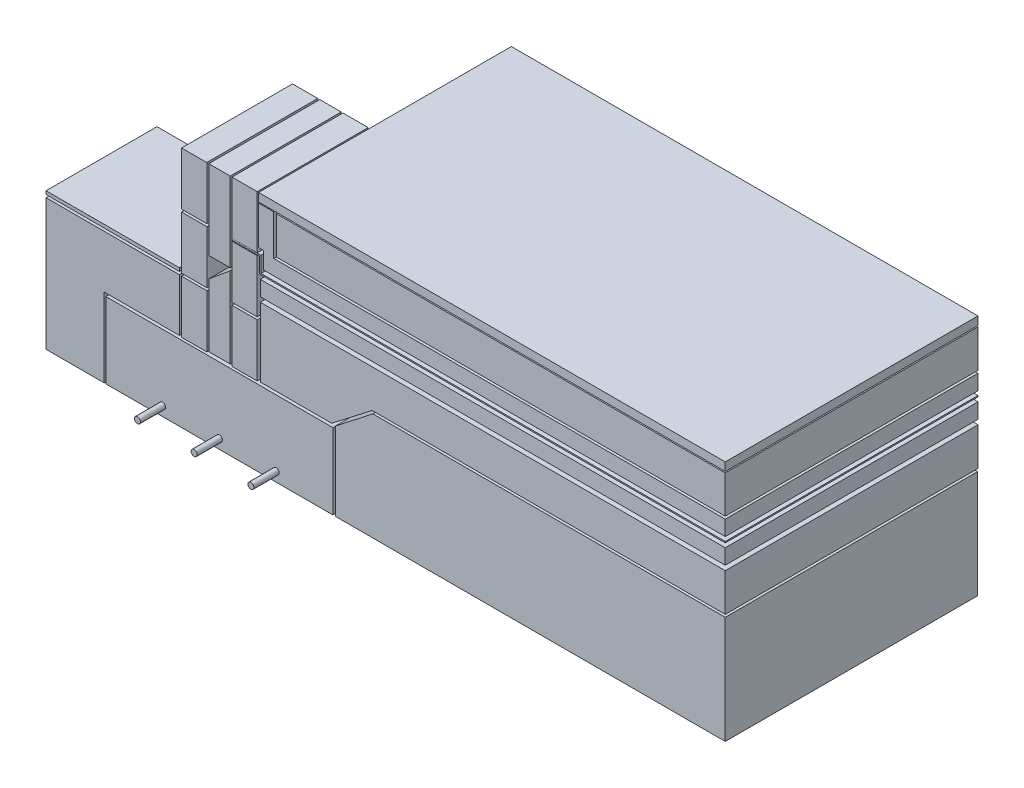
SolidWorks part; units mm, degrees
ref_plane "Front Plane" through (0, 0, 0) normal (0, 0, 1) x (1, 0, 0)
ref_plane "Top Plane" through (0, 0, 0) normal (0, 1, 0) x (1, 0, 0)
ref_plane "Right Plane" through (0, 0, 0) normal (1, 0, 0) x (0, 0, -1)
sketch "Sketch1" plane through (0, 0, 0) normal (0, 0, 1) x (1, 0, 0)
  line L0 (0, 0) -> (900, 300) construction
  line L1 (0, 0) -> (900, 0)
  line L2 (0, 0) -> (0, 300)
  line L3 (0, 300) -> (900, 300)
  line L4 (900, 0) -> (900, 300)
  line L5 (0, 300) -> (900, 0) construction
  line L6 (450, 150) -> (450, -149.0369) construction
  dimension "D1" = 900
  dimension "D2" = 300
extrude "Extrude1" add sketch "Sketch1" against normal blind 440
ref_plane "Plane1" through (0, 310, 0) normal (0, 1, 0) x (-1, 0, 0)
sketch "Sketch2" plane through (0, 310, 0) normal (0, 1, 0) x (-1, 0, 0)
  line L0 (-900, 0) -> (0, 0) construction
  line L1 (-600, -440) -> (-500, -440)
  line L2 (-600, -440) -> (-600, 0)
  line L3 (-600, 0) -> (-500, 0)
  line L4 (-500, -440) -> (-500, 0)
  line L5 (-900, -440) -> (-900, 0) construction
  dimension "D1" = 440
  dimension "D2" = 100
  dimension "D3" = 300
extrude "Extrude2" add sketch "Sketch2" along normal blind 210
sketch "Sketch3" plane through (0, 310, 0) normal (0, 1, 0) x (-1, 0, 0)
  line L0 (-900, 0) -> (0, 0) construction
  line L1 (-400, 0) -> (-300, 0)
  line L2 (-400, 0) -> (-400, -440)
  line L3 (-400, -440) -> (-300, -440)
  line L4 (-300, 0) -> (-300, -440)
  line L5 (-500, -440) -> (-500, 0) construction
  dimension "D1" = 440
  dimension "D2" = 100
  dimension "D3" = 100
extrude "Extrude3" add sketch "Sketch3" along normal blind 210
ref_plane "Plane2" through (0, 530, 0) normal (0, 1, 0) x (-1, 0, 0)
sketch "Sketch4" plane through (0, 530, 0) normal (0, 1, 0) x (-1, 0, 0)
  line L0 (-900, 0) -> (0, 0) construction
  line L1 (-500, 0) -> (-600, 0)
  line L2 (-500, 0) -> (-500, -440)
  line L3 (-500, -440) -> (-600, -440)
  line L4 (-600, 0) -> (-600, -440)
  line L5 (-900, -440) -> (-900, 0) construction
  line L6 (-900, -440) -> (0, -440) construction
  line L7 (-300, 0) -> (-400, 0)
  line L8 (-300, 0) -> (-300, -440)
  line L9 (-300, -440) -> (-400, -440)
  line L10 (-400, 0) -> (-400, -440)
  line L11 (0, -440) -> (0, 0) construction
  dimension "D1" = 440
  dimension "D2" = 100
  dimension "D3" = 300
  dimension "D4" = 440
  dimension "D5" = 100
  dimension "D6" = 300
extrude "Extrude4" add sketch "Sketch4" along normal blind 210
ref_plane "Plane3" through (0, 750, 0) normal (0, 1, 0) x (-1, 0, 0)
sketch "Sketch5" plane through (0, 750, 0) normal (0, 1, 0) x (-1, 0, 0)
  line L0 (-900, -440) -> (-900, 0) construction
  line L1 (-500, 0) -> (-600, 0)
  line L2 (-500, 0) -> (-500, -440)
  line L3 (-500, -440) -> (-600, -440)
  line L4 (-600, 0) -> (-600, -440)
  line L5 (-500, 0) -> (-600, 0) construction
  line L6 (0, -440) -> (0, 0) construction
  line L7 (-300, 0) -> (-400, 0)
  line L8 (-300, 0) -> (-300, -440)
  line L9 (-300, -440) -> (-400, -440)
  line L10 (-400, 0) -> (-400, -440)
  line L11 (-300, 0) -> (-400, 0) construction
  dimension "D1" = 100
  dimension "D2" = 440
  dimension "D3" = 300
  dimension "D4" = 440
  dimension "D5" = 100
  dimension "D6" = 300
extrude "Extrude5" add sketch "Sketch5" along normal blind 210
ref_plane "Plane4" through (0, 0, 0) normal (0, 0, 1) x (1, 0, 0)
sketch "Sketch8" plane through (0, 0, 0) normal (0, 0, 1) x (1, 0, 0)
  line L0 (612.3373, 312.3392) -> (612.3373, 586.3969)
  line L1 (612.3373, 586.3969) -> (2455.482, 586.3969)
  line L2 (2455.482, 586.3969) -> (2455.482, 436.3969)
  line L3 (2455.482, 436.3969) -> (1055.482, 436.3969)
  line L4 (1055.482, 436.3969) -> (895.482, 312.3392)
  line L5 (895.482, 312.3392) -> (612.3373, 312.3392)
  dimension "D1" = 150
  dimension "D2" = 1400
  dimension "D3" = 160
  dimension "D4" = 283.1447
  dimension "D5" = 274.0577
extrude "Extrude7" add sketch "Sketch8" against normal blind 1002 separate body
sketch "Sketch9" plane through (0, 0, 0) normal (0, 0, 1) x (1, 0, 0)
  line L0 (493.0445, 314.5374) -> (493.0445, 634.5374)
  line L1 (493.0445, 634.5374) -> (408.0445, 564.5374)
  line L2 (408.0445, 564.5374) -> (408.0445, 314.5374)
  line L3 (408.0445, 314.5374) -> (493.0445, 314.5374)
  dimension "D1" = 320
  dimension "D2" = 250
  dimension "D3" = 85
extrude "Extrude8" add sketch "Sketch9" against normal blind 440
sketch "Sketch10" plane through (0, 0, 0) normal (0, 0, 1) x (1, 0, 0)
  line L1 (493.0445, 960) -> (408.0445, 960)
  line L2 (493.0445, 960) -> (493.0445, 644.9402)
  line L3 (493.0445, 644.9402) -> (408.0445, 644.9402)
  line L4 (408.0445, 960) -> (408.0445, 644.9402)
  dimension "D1" = 85
  dimension "D2" = 315.0598
extrude "Extrude9" add sketch "Sketch10" against normal blind 440
sketch "Sketch12" plane through (0, 0, 0) normal (0, 0, 1) x (1, 0, 0)
  line L0 (910, 0) -> (910, 310.3325)
  line L1 (910, 310.3325) -> (1058.6167, 426.3969)
  line L2 (1058.6167, 426.3969) -> (2455.482, 426.3969)
  line L3 (2455.482, 426.3969) -> (2455.482, 0)
  line L4 (2455.482, 0) -> (910, 0)
  line L5 (900, 0) -> (900, 300) construction
  line L6 (895.482, 312.3392) -> (1055.482, 436.3969) construction
  line L7 (1055.482, 436.3969) -> (2455.482, 436.3969) construction
  line L8 (2455.482, 436.3969) -> (2455.482, 586.3969) construction
  point P2 (900, 150)
  dimension "D1" = 10
  dimension "D2" = 0.2
  dimension "D3" = 10
  dimension "D4" = 1396.8653
extrude "Extrude11" add sketch "Sketch12" against normal blind 1000 separate body
sketch "Sketch14" plane through (0, 0, 0) normal (0, 0, 1) x (1, 0, 0)
  line L0 (612.3373, 586.3969) -> (612.3373, 312.3392) construction
  line L1 (612.3373, 605.0982) -> (2455.482, 605.0982)
  line L2 (612.3373, 605.0982) -> (612.3373, 665.0982)
  line L3 (612.3373, 665.0982) -> (2455.482, 665.0982)
  line L4 (2455.482, 605.0982) -> (2455.482, 665.0982)
  line L5 (2455.482, 436.3969) -> (2455.482, 586.3969) construction
  dimension "D1" = 60
extrude "Extrude12" add sketch "Sketch14" against normal up to vertex (1002 mm away) separate body
sketch "Sketch15" plane through (0, 0, 0) normal (0, 0, 1) x (1, 0, 0)
  line L0 (610, 681.769) -> (610, 743.5276)
  line L1 (610, 743.5276) -> (499.1337, 743.5276)
  line L2 (610, 681.769) -> (2455.482, 681.769)
  line L3 (2455.482, 681.769) -> (2455.482, 686.769)
  line L4 (2455.482, 686.769) -> (633.6467, 686.769)
  line L5 (615, 749.3027) -> (500, 750)
  line L7 (500, 750) -> (499.1337, 743.5276)
  line L8 (615, 749.3027) -> (615, 686.769)
  line L9 (615, 686.769) -> (633.6467, 686.769)
  line L10 (600, 740) -> (600, 530) construction
  line L11 (2455.482, 605.0982) -> (2455.482, 665.0982) construction
  dimension "D1" = 0.347
  dimension "D2" = 5
  dimension "D3" = 10
  dimension "D4" = 5
extrude "Extrude13" add sketch "Sketch15" against normal up to vertex (1002 mm away) separate body
sketch "Sketch16" plane through (0, 0, 0) normal (0, 0, 1) x (1, 0, 0)
  line L0 (2455.482, 703.4337) -> (625.5628, 703.4337)
  line L1 (625.5628, 703.4337) -> (625.5628, 770.7278)
  line L2 (665.5161, 763.4337) -> (665.5161, 923.4337)
  line L3 (2455.482, 763.4337) -> (2455.482, 703.4337)
  line L4 (605.5161, 923.4337) -> (665.5161, 923.4337)
  line L5 (605.5161, 770.7278) -> (605.5161, 923.4337)
  line L6 (605.5161, 770.7278) -> (625.5628, 770.7278)
  line L8 (665.5161, 763.4337) -> (2455.482, 763.4337)
  dimension "D1" = 60
  dimension "D2" = 220
  dimension "D3" = 60
extrude "Extrude14" add sketch "Sketch16" against normal up to vertex (1002 mm away) separate body
sketch "Sketch17" plane through (0, 0, 0) normal (0, 0, 1) x (1, 0, 0)
  line L0 (665.5161, 763.4337) -> (665.5161, 923.4337) construction
  line L1 (675.5161, 922.1211) -> (2455.482, 922.1211)
  line L2 (675.5161, 922.1211) -> (675.5161, 773.4337)
  line L3 (675.5161, 773.4337) -> (2455.482, 773.4337)
  line L4 (2455.482, 922.1211) -> (2455.482, 773.4337)
  line L5 (2455.482, 763.4337) -> (665.5161, 763.4337) construction
  line L6 (2455.482, 703.4337) -> (2455.482, 763.4337) construction
  dimension "D1" = 10
  dimension "D2" = 10
extrude "Extrude15" add sketch "Sketch17" against normal up to vertex (1002 mm away) separate body
sketch "Sketch18" plane through (0, 0, 0) normal (0, 0, 1) x (1, 0, 0)
  circle A0 centre (225, 37.8059) radius 12
  circle A1 centre (450, 37.8059) radius 12
  circle A2 centre (675, 37.8059) radius 12
  dimension "D2" = 225
  dimension "D4" = 24
  dimension "D3" = 225
extrude "Extrude16" add sketch "Sketch18" along normal blind 100
sketch "Sketch19" plane through (0, 0, 0) normal (0, 0, 1) x (1, 0, 0)
  line L0 (605.5161, 923.4337) -> (605.5161, 770.7278) construction
  line L1 (605.5161, 960) -> (2455.482, 960)
  line L2 (605.5161, 960) -> (605.5161, 927.1211)
  line L3 (605.5161, 927.1211) -> (2455.482, 927.1211)
  line L4 (2455.482, 960) -> (2455.482, 927.1211)
  line L5 (2455.482, 773.4337) -> (2455.482, 922.1211) construction
  line L6 (2455.482, 922.1211) -> (675.5161, 922.1211) construction
  line L7 (500, 960) -> (600, 960) construction
  dimension "D1" = 5
extrude "Extrude17" add sketch "Sketch19" against normal up to vertex (1002 mm away) separate body
sketch "Sketch20" plane through (0, 0, 0) normal (0, 0, 1) x (1, 0, 0)
  line L0 (291.3563, 312.0016) -> (291.3563, 520.5776)
  line L1 (291.3563, 520.5776) -> (-237.3223, 520.5776)
  line L2 (-237.3223, 520.5776) -> (-237.3223, 0)
  line L3 (-237.3223, 0) -> (-6.7596, 0)
  line L4 (-6.7596, 0) -> (-6.7596, 312.0016)
  line L5 (-6.7596, 312.0016) -> (291.3563, 312.0016)
extrude "Extrude18" add sketch "Sketch20" against normal up to vertex (440 mm away) separate body
sketch "Sketch21" plane through (0, 0, 0) normal (0, 0, 1) x (1, 0, 0)
  line L1 (-237.3223, 531.5522) -> (291.3563, 531.5522)
  line L2 (-237.3223, 531.5522) -> (-237.3223, 544.4531)
  line L3 (-237.3223, 544.4531) -> (291.3563, 544.4531)
  line L4 (291.3563, 531.5522) -> (291.3563, 544.4531)
extrude "Extrude19" add sketch "Sketch21" against normal up to vertex (440 mm away) separate body
